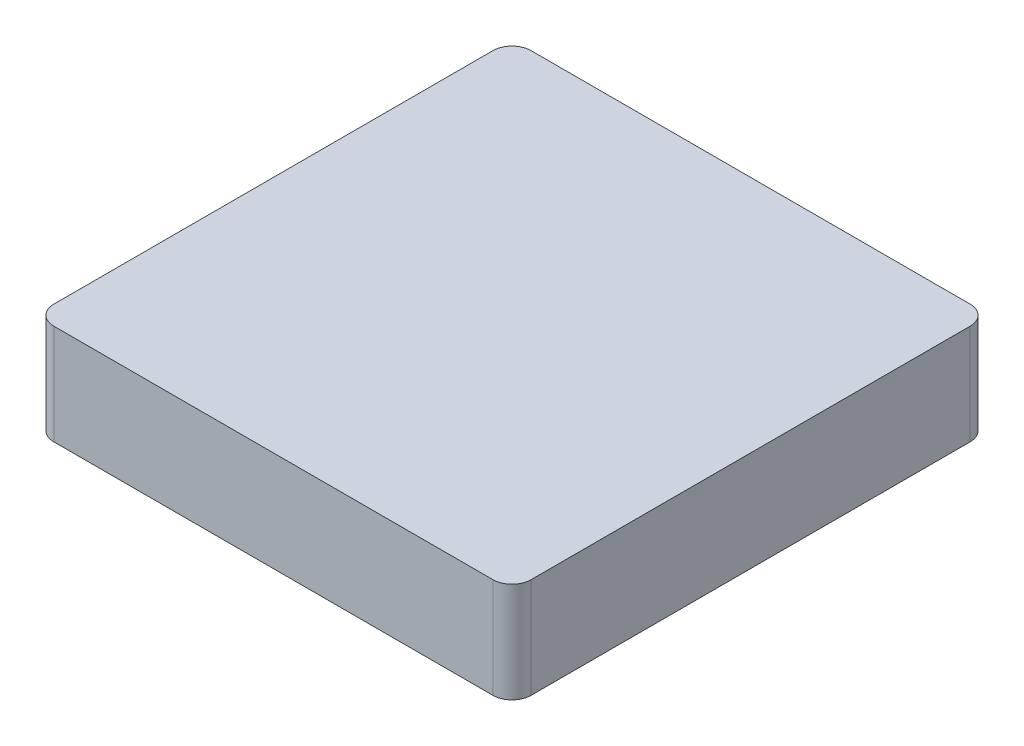
SolidWorks part; units mm, degrees
ref_plane "前视基准面" through (0, 0, 0) normal (0, 0, 1) x (1, 0, 0)
ref_plane "上视基准面" through (0, 0, 0) normal (0, 1, 0) x (1, 0, 0)
ref_plane "右视基准面" through (0, 0, 0) normal (1, 0, 0) x (0, 0, -1)
sketch "草图1" plane through (0, 0, 0) normal (0, 1, 0) x (1, 0, 0)
  line L1 (-25, 25) -> (25, 25)
  line L2 (-25, 25) -> (-25, -25)
  line L3 (-25, -25) -> (25, -25)
  line L4 (25, 25) -> (25, -25)
  line L5 (-25, 25) -> (25, -25) construction
  line L6 (-25, -25) -> (25, 25) construction
  point P0 (0, 0)
extrude "凸台-拉伸1" add sketch "草图1" along normal blind 10
sketch "草图2" plane through (0, 10, 0) normal (0, 1, 0) x (1, 0, 0)
  line L1 (-25, 25) -> (25, 25)
  line L2 (-25, 25) -> (-25, -25)
  line L3 (-25, -25) -> (25, -25)
  line L4 (25, 25) -> (25, -25)
  line L5 (-25, 25) -> (25, -25) construction
  line L6 (-25, -25) -> (25, 25) construction
  point P0 (0, 0)
extrude "凸台-拉伸2" add sketch "草图2" along normal blind 0.5
fillet "圆角1" radius 2 4 edges at (25, 5.25, -25) (25, 5.25, 25) (-25, 5.25, 25) (-25, 5.25, -25)
